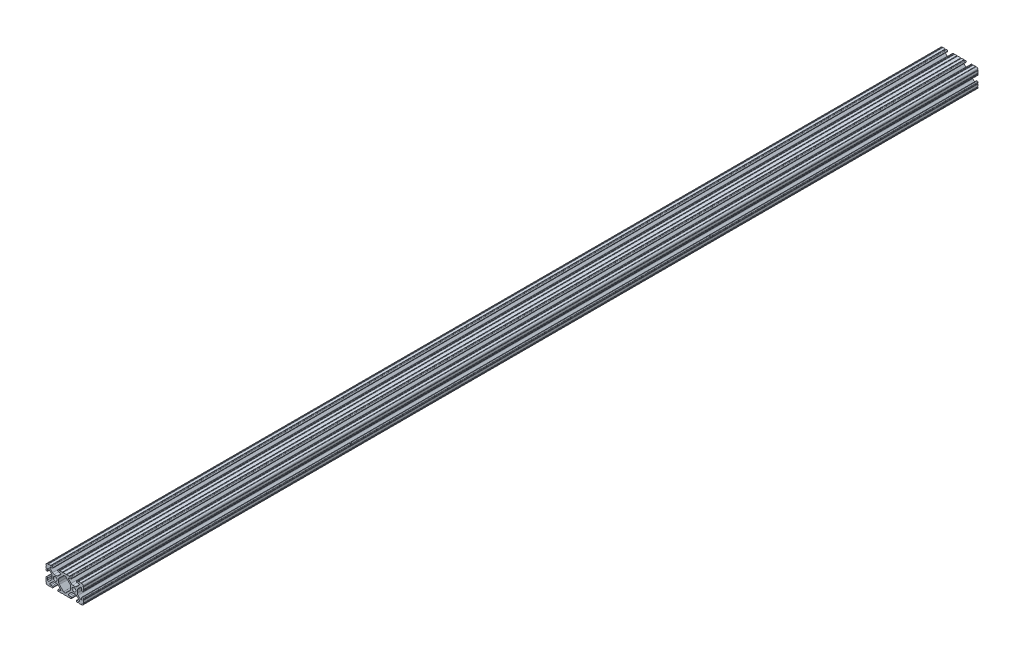
SolidWorks part; units mm, degrees
ref_plane "Front Plane" through (0, 0, 0) normal (0, 0, 1) x (1, 0, 0)
ref_plane "Top Plane" through (0, 0, 0) normal (0, 1, 0) x (1, 0, 0)
ref_plane "Right Plane" through (0, 0, 0) normal (1, 0, 0) x (0, 0, -1)
sketch "Sketch1" plane through (0, 0, 0) normal (0, 0, 1) x (1, 0, 0)
  line L0 (-7.2595, -3.8694) -> (-1.5457, -9.5728)
  line L1 (-8.1915, 1.6223) -> (-8.1915, -1.6223)
  line L2 (-1.504, 9.5765) -> (-7.252, 3.8768)
  line L3 (0.5515, 10.033) -> (-0.3952, 10.033)
  line L4 (7.2829, 3.8459) -> (1.6756, 9.5611)
  line L5 (8.1915, -1.6223) -> (8.1915, 1.6223)
  line L6 (1.5457, -9.5728) -> (7.2595, -3.8694)
  line L7 (-0.4332, -10.033) -> (0.4332, -10.033)
  line L8 (18.0171, 12.7) -> (16.9875, 12.7)
  line L9 (15.9385, 11.651) -> (15.9385, 11.5392)
  line L10 (16.9875, 10.4902) -> (19.1164, 10.4902)
  line L11 (19.8441, 8.7652) -> (16.619, 5.4551)
  line L12 (14.3449, 4.4958) -> (11.0833, 4.4958)
  line L13 (8.817, 5.4472) -> (5.5642, 8.7627)
  line L14 (6.2894, 10.4902) -> (8.4125, 10.4902)
  line L15 (9.4615, 11.5392) -> (9.4615, 11.651)
  line L16 (8.4125, 12.7) -> (7.3829, 12.7)
  line L17 (6.3669, 12.7) -> (3.1496, 12.7)
  line L18 (2.1336, 12.7) -> (-2.1336, 12.7)
  line L19 (-3.1496, 12.7) -> (-6.3669, 12.7)
  line L20 (-7.3829, 12.7) -> (-8.4125, 12.7)
  line L21 (-9.4615, 11.651) -> (-9.4615, 11.5392)
  line L22 (-8.4125, 10.4902) -> (-6.2836, 10.4902)
  line L23 (-5.5326, 8.6661) -> (-8.81, 5.4163)
  line L24 (-11.0455, 4.4958) -> (-14.3545, 4.4958)
  line L25 (-16.59, 5.4163) -> (-19.8674, 8.6661)
  line L26 (-19.1164, 10.4902) -> (-16.9875, 10.4902)
  line L27 (-15.9385, 11.5392) -> (-15.9385, 11.651)
  line L28 (-16.9875, 12.7) -> (-18.0171, 12.7)
  line L29 (-19.0331, 12.7) -> (-22.2504, 12.7)
  line L30 (-25.4, 9.5504) -> (-25.4, 6.3331)
  line L31 (-25.4, 5.3171) -> (-25.4, 4.2375)
  line L32 (-24.401, 3.2385) -> (-24.2392, 3.2385)
  line L33 (-23.1902, 4.2875) -> (-23.1902, 6.3347)
  line L34 (-21.434, 7.0665) -> (-18.148, 3.8082)
  line L35 (-17.2085, 1.5536) -> (-17.2085, -1.6952)
  line L36 (-18.1405, -3.9423) -> (-21.4316, -7.2274)
  line L37 (-23.1902, -6.498) -> (-23.1902, -4.2875)
  line L38 (-24.2392, -3.2385) -> (-24.351, -3.2385)
  line L39 (-25.4, -4.2875) -> (-25.4, -5.3171)
  line L40 (-25.4, -6.3331) -> (-25.4, -9.5504)
  line L41 (-22.2504, -12.7) -> (-19.0331, -12.7)
  line L42 (-18.0171, -12.7) -> (-16.9875, -12.7)
  line L43 (-15.9384, -11.651) -> (-15.9384, -11.5392)
  line L44 (-16.9875, -10.4902) -> (-19.1164, -10.4902)
  line L45 (-19.8341, -8.7551) -> (-16.4966, -5.4237)
  line L46 (-14.2536, -4.4958) -> (-11.1464, -4.4958)
  line L47 (-8.9034, -5.4237) -> (-5.5659, -8.7551)
  line L48 (-6.2836, -10.4902) -> (-8.4125, -10.4902)
  line L49 (-9.4616, -11.5392) -> (-9.4616, -11.651)
  line L50 (-8.4125, -12.7) -> (-7.3829, -12.7)
  line L51 (-6.3669, -12.7) -> (-3.1496, -12.7)
  line L52 (-2.1336, -12.7) -> (2.1336, -12.7)
  line L53 (3.1496, -12.7) -> (6.3669, -12.7)
  line L54 (7.3829, -12.7) -> (8.4125, -12.7)
  line L55 (9.4616, -11.651) -> (9.4616, -11.5392)
  line L56 (8.4125, -10.4902) -> (6.2894, -10.4902)
  line L57 (5.4807, -8.5353) -> (8.5979, -5.4237)
  line L58 (10.8409, -4.4958) -> (14.1026, -4.4958)
  line L59 (16.1879, -5.2766) -> (19.8682, -8.4822)
  line L60 (19.1164, -10.4902) -> (16.9875, -10.4902)
  line L61 (15.9384, -11.5392) -> (15.9384, -11.651)
  line L62 (16.9875, -12.7) -> (18.0171, -12.7)
  line L63 (19.0331, -12.7) -> (22.2504, -12.7)
  line L64 (25.4, -9.5504) -> (25.4, -6.3331)
  line L65 (25.4, -5.3171) -> (25.4, -4.2375)
  line L66 (24.401, -3.2385) -> (24.1892, -3.2385)
  line L67 (23.1902, -4.2375) -> (23.1902, -6.1559)
  line L68 (21.584, -6.8869) -> (18.2982, -4.025)
  line L69 (17.2085, -1.6308) -> (17.2085, 1.6308)
  line L70 (18.1094, 3.8465) -> (21.5263, 7.3534)
  line L71 (23.1902, 6.6769) -> (23.1902, 4.2375)
  line L72 (24.1892, 3.2385) -> (24.401, 3.2385)
  line L73 (25.4, 4.2375) -> (25.4, 5.3171)
  line L74 (25.4, 6.3332) -> (25.4, 9.5504)
  line L75 (22.2504, 12.7) -> (19.0331, 12.7)
  circle A0 centre (-12.7, 0) radius 2.6035
  circle A1 centre (12.7, 0) radius 2.6035
  arc A2 (-1.5457, -9.5728) -> (-0.4332, -10.033) centre (-0.4332, -8.4582) ccw
  arc A3 (-8.1915, -1.6223) -> (-7.2595, -3.8694) centre (-5.0165, -1.6223) ccw
  arc A4 (-7.252, 3.8768) -> (-8.1915, 1.6223) centre (-5.0165, 1.6223) ccw
  arc A5 (-0.3952, 10.033) -> (-1.504, 9.5765) centre (-0.3952, 8.4582) ccw
  arc A6 (1.6756, 9.5611) -> (0.5515, 10.033) centre (0.5515, 8.4582) ccw
  arc A7 (8.1915, 1.6223) -> (7.2829, 3.8459) centre (5.0165, 1.6223) ccw
  arc A8 (7.2595, -3.8694) -> (8.1915, -1.6223) centre (5.0165, -1.6223) ccw
  arc A9 (0.4332, -10.033) -> (1.5457, -9.5728) centre (0.4332, -8.4582) ccw
  arc A10 (18.0171, 12.7) -> (19.0331, 12.7) centre (18.5251, 12.7) ccw
  arc A11 (16.9875, 12.7) -> (15.9385, 11.651) centre (16.9875, 11.651) ccw
  arc A12 (15.9385, 11.5392) -> (16.9875, 10.4902) centre (16.9875, 11.5392) ccw
  arc A13 (19.8441, 8.7652) -> (19.1164, 10.4902) centre (19.1164, 9.4742) ccw
  arc A14 (14.3449, 4.4958) -> (16.619, 5.4551) centre (14.3449, 7.6708) ccw
  arc A15 (8.817, 5.4472) -> (11.0833, 4.4958) centre (11.0833, 7.6708) ccw
  arc A16 (6.2894, 10.4902) -> (5.5642, 8.7627) centre (6.2894, 9.4742) ccw
  arc A17 (8.4125, 10.4902) -> (9.4615, 11.5392) centre (8.4125, 11.5392) ccw
  arc A18 (9.4615, 11.651) -> (8.4125, 12.7) centre (8.4125, 11.651) ccw
  arc A19 (6.3669, 12.7) -> (7.3829, 12.7) centre (6.8749, 12.7) ccw
  arc A20 (2.1336, 12.7) -> (3.1496, 12.7) centre (2.6416, 12.7) ccw
  arc A21 (-3.1496, 12.7) -> (-2.1336, 12.7) centre (-2.6416, 12.7) ccw
  arc A22 (-7.3829, 12.7) -> (-6.3669, 12.7) centre (-6.8749, 12.7) ccw
  arc A23 (-8.4125, 12.7) -> (-9.4615, 11.651) centre (-8.4125, 11.651) ccw
  arc A24 (-9.4615, 11.5392) -> (-8.4125, 10.4902) centre (-8.4125, 11.5392) ccw
  arc A25 (-5.5326, 8.6661) -> (-6.2836, 10.4902) centre (-6.2836, 9.4235) ccw
  arc A26 (-11.0455, 4.4958) -> (-8.81, 5.4163) centre (-11.0455, 7.6708) ccw
  arc A27 (-16.59, 5.4163) -> (-14.3545, 4.4958) centre (-14.3545, 7.6708) ccw
  arc A28 (-19.1164, 10.4902) -> (-19.8674, 8.6661) centre (-19.1164, 9.4235) ccw
  arc A29 (-16.9875, 10.4902) -> (-15.9385, 11.5392) centre (-16.9875, 11.5392) ccw
  arc A30 (-15.9385, 11.651) -> (-16.9875, 12.7) centre (-16.9875, 11.651) ccw
  arc A31 (-19.0331, 12.7) -> (-18.0171, 12.7) centre (-18.5251, 12.7) ccw
  arc A32 (-23.2664, 12.6998) -> (-22.2504, 12.7) centre (-22.7584, 12.7) ccw
  arc A33 (-23.2664, 12.6998) -> (-25.3998, 10.5664) centre (-23.2918, 10.5918) ccw
  arc A34 (-25.4, 9.5504) -> (-25.3998, 10.5664) centre (-25.4, 10.0584) ccw
  arc A35 (-25.4, 5.3171) -> (-25.4, 6.3331) centre (-25.4, 5.8251) ccw
  arc A36 (-25.4, 4.2375) -> (-24.401, 3.2385) centre (-24.401, 4.2375) ccw
  arc A37 (-24.2392, 3.2385) -> (-23.1902, 4.2875) centre (-24.2392, 4.2875) ccw
  arc A38 (-21.434, 7.0665) -> (-23.1902, 6.3347) centre (-22.1596, 6.3347) ccw
  arc A39 (-17.2085, 1.5536) -> (-18.148, 3.8082) centre (-20.3835, 1.5536) ccw
  arc A40 (-18.1405, -3.9423) -> (-17.2085, -1.6952) centre (-20.3835, -1.6952) ccw
  arc A41 (-23.1902, -6.498) -> (-21.4316, -7.2274) centre (-22.1596, -6.498) ccw
  arc A42 (-23.1902, -4.2875) -> (-24.2392, -3.2385) centre (-24.2392, -4.2875) ccw
  arc A43 (-24.351, -3.2385) -> (-25.4, -4.2875) centre (-24.351, -4.2875) ccw
  arc A44 (-25.4, -6.3331) -> (-25.4, -5.3171) centre (-25.4, -5.8251) ccw
  arc A45 (-25.3998, -10.5664) -> (-25.4, -9.5504) centre (-25.4, -10.0584) ccw
  arc A46 (-25.3998, -10.5664) -> (-23.2664, -12.6998) centre (-23.2918, -10.5918) ccw
  arc A47 (-22.2504, -12.7) -> (-23.2664, -12.6998) centre (-22.7584, -12.7) ccw
  arc A48 (-18.0171, -12.7) -> (-19.0331, -12.7) centre (-18.5251, -12.7) ccw
  arc A49 (-16.9875, -12.7) -> (-15.9384, -11.651) centre (-16.9875, -11.651) ccw
  arc A50 (-15.9384, -11.5392) -> (-16.9875, -10.4902) centre (-16.9875, -11.5392) ccw
  arc A51 (-19.8341, -8.7551) -> (-19.1164, -10.4902) centre (-19.1164, -9.4742) ccw
  arc A52 (-14.2536, -4.4958) -> (-16.4966, -5.4237) centre (-14.2536, -7.6708) ccw
  arc A53 (-8.9034, -5.4237) -> (-11.1464, -4.4958) centre (-11.1464, -7.6708) ccw
  arc A54 (-6.2836, -10.4902) -> (-5.5659, -8.7551) centre (-6.2836, -9.4742) ccw
  arc A55 (-8.4125, -10.4902) -> (-9.4616, -11.5392) centre (-8.4125, -11.5392) ccw
  arc A56 (-9.4616, -11.651) -> (-8.4125, -12.7) centre (-8.4125, -11.651) ccw
  arc A57 (-6.3669, -12.7) -> (-7.3829, -12.7) centre (-6.8749, -12.7) ccw
  arc A58 (-2.1336, -12.7) -> (-3.1496, -12.7) centre (-2.6416, -12.7) ccw
  arc A59 (3.1496, -12.7) -> (2.1336, -12.7) centre (2.6416, -12.7) ccw
  arc A60 (7.3829, -12.7) -> (6.3669, -12.7) centre (6.8749, -12.7) ccw
  arc A61 (8.4125, -12.7) -> (9.4616, -11.651) centre (8.4125, -11.651) ccw
  arc A62 (9.4616, -11.5392) -> (8.4125, -10.4902) centre (8.4125, -11.5392) ccw
  arc A63 (5.4807, -8.5353) -> (6.2894, -10.4902) centre (6.2894, -9.3455) ccw
  arc A64 (10.8409, -4.4958) -> (8.5979, -5.4237) centre (10.8409, -7.6708) ccw
  arc A65 (16.1879, -5.2766) -> (14.1026, -4.4958) centre (14.1026, -7.6708) ccw
  arc A66 (19.1164, -10.4902) -> (19.8682, -8.4822) centre (19.1164, -9.3455) ccw
  arc A67 (16.9875, -10.4902) -> (15.9384, -11.5392) centre (16.9875, -11.5392) ccw
  arc A68 (15.9384, -11.651) -> (16.9875, -12.7) centre (16.9875, -11.651) ccw
  arc A69 (19.0331, -12.7) -> (18.0171, -12.7) centre (18.5251, -12.7) ccw
  arc A70 (23.2664, -12.6998) -> (22.2504, -12.7) centre (22.7584, -12.7) ccw
  arc A71 (23.2664, -12.6998) -> (25.3998, -10.5664) centre (23.2918, -10.5918) ccw
  arc A72 (25.4, -9.5504) -> (25.3998, -10.5664) centre (25.4, -10.0584) ccw
  arc A73 (25.4, -5.3171) -> (25.4, -6.3331) centre (25.4, -5.8251) ccw
  arc A74 (25.4, -4.2375) -> (24.401, -3.2385) centre (24.401, -4.2375) ccw
  arc A75 (24.1892, -3.2385) -> (23.1902, -4.2375) centre (24.1892, -4.2375) ccw
  arc A76 (21.584, -6.8869) -> (23.1902, -6.1559) centre (22.2207, -6.1559) ccw
  arc A77 (17.2085, -1.6308) -> (18.2982, -4.025) centre (20.3835, -1.6308) ccw
  arc A78 (18.1094, 3.8465) -> (17.2085, 1.6308) centre (20.3835, 1.6308) ccw
  arc A79 (23.1902, 6.6769) -> (21.5263, 7.3534) centre (22.2207, 6.6769) ccw
  arc A80 (23.1902, 4.2375) -> (24.1892, 3.2385) centre (24.1892, 4.2375) ccw
  arc A81 (24.401, 3.2385) -> (25.4, 4.2375) centre (24.401, 4.2375) ccw
  arc A82 (25.4, 6.3332) -> (25.4, 5.3171) centre (25.4, 5.8251) ccw
  arc A83 (25.3998, 10.5664) -> (25.4, 9.5504) centre (25.4, 10.0584) ccw
  arc A84 (25.3998, 10.5664) -> (23.2664, 12.6998) centre (23.2918, 10.5918) ccw
  arc A85 (22.2504, 12.7) -> (23.2664, 12.6998) centre (22.7584, 12.7) ccw
  point P248 (0, 10.033)
extrude "Boss-Extrude1" add sketch "Sketch1" along normal mid plane 1219.2
sketch "Sketch2" plane through (17.2085, 0, 0) normal (1, 0, 0) x (0, 0, -1)
  line L1 (609.6, -1.6308) -> (609.6, 1.6308) construction
  line L2 (0, 0) -> (0, 191.3427) construction
  circle A0 centre (244.47, 0) radius 3.5
  circle A1 centre (-244.47, 0) radius 3.5
  dimension "D1" = 7
  dimension "D2" = 365.13
extrude "Cut-Extrude1" cut sketch "Sketch2" against normal through all both and the other way through all
